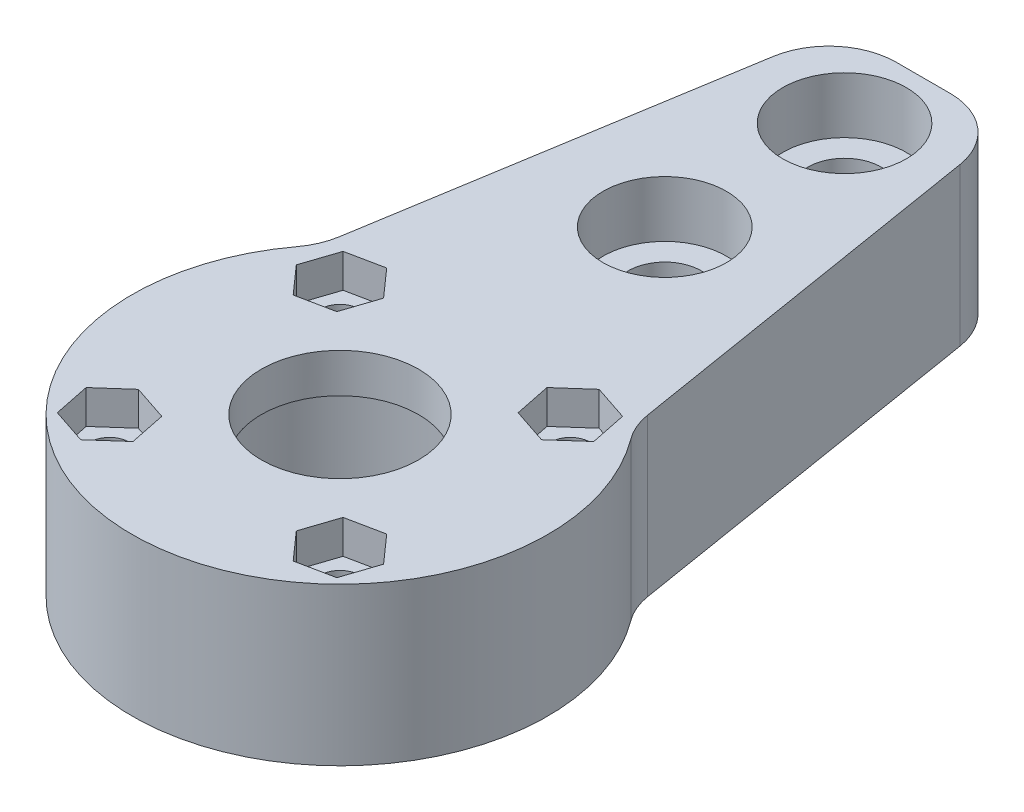
SolidWorks part; units mm, degrees
ref_plane "Front Plane" through (0, 0, 0) normal (0, 0, 1) x (1, 0, 0)
ref_plane "Top Plane" through (0, 0, 0) normal (0, 1, 0) x (1, 0, 0)
ref_plane "Right Plane" through (0, 0, 0) normal (1, 0, 0) x (0, 0, -1)
sketch "Sketch1" plane through (0, 0, 0) normal (0, 1, 0) x (1, 0, 0)
  line L0 (0, 0) -> (0, 16.3631) construction
  line L1 (-7.5, 16.9115) -> (7.5, 16.9115) construction
  line L2 (-7.5, 16.9115) -> (-7.5, 51.9115) construction
  line L3 (-7.5, 51.9115) -> (7.5, 51.9115)
  line L4 (7.5, 51.9115) -> (7.5, 16.9115) construction
  line L5 (12.7, 20) -> (-12.7, 20) construction
  line L6 (12.7721, 19.5576) -> (8.4504, 46.0788) construction
  line L7 (-12.7721, 19.5576) -> (-8.4504, 46.0788) construction
  line L8 (13.9857, 12.1099) -> (7.5, 51.9115)
  line L9 (-13.9857, 12.1099) -> (-7.5, 51.9115)
  circle A0 centre (0, 0) radius 7
  circle A1 centre (0, 0) radius 18.5 construction
  arc A2 (13.9857, 12.1099) -> (-13.9857, 12.1099) centre (0, 0) cw
  point P8 (0, 16.9115)
  point P15 (0, 20)
  dimension "D1" = 14
  dimension "D2" = 37
  dimension "D3" = 15
  dimension "D4" = 35
  dimension "D5" = 25.4
  dimension "D6" = 20
extrude "Boss-Extrude1" add sketch "Sketch1" along normal blind 14
sketch "Sketch2" plane through (0, 0, 0) normal (0, -1, 0) x (1, 0, 0)
  circle A0 centre (0, 0) radius 11.075
  dimension "D1" = 22.15
extrude "Cut-Extrude1" cut sketch "Sketch2" against normal blind 10.5
sketch "Sketch4" plane through (0, 0, 0) normal (0, -1, 0) x (1, 0, 0)
  line L0 (0, 0) -> (10.253, 10.253) construction
  line L1 (0, 0) -> (0, 5.0875) construction
  circle A1 centre (10.253, 10.253) radius 1.75
  circle A2 centre (10.253, -10.253) radius 1.75
  circle A3 centre (-10.253, -10.253) radius 1.75
  circle A4 centre (-10.253, 10.253) radius 1.75
  point P15 (0, 0)
  dimension "D1" = 45
  dimension "D2" = 3.5
  dimension "D3" = 14.5
  dimension "D4" = 4
extrude "Cut-Extrude4" cut sketch "Sketch4" against normal through all
sketch "Sketch5" plane through (0, 14, 0) normal (0, 1, 0) x (1, 0, 0)
  line L0 (13.3754, 9.2133) -> (12.7147, 12.4372)
  line L1 (-9.2133, 13.3754) -> (-12.4372, 12.7147)
  line L2 (-12.4372, 12.7147) -> (-13.4769, 9.5924)
  line L3 (-13.4769, 9.5924) -> (-11.2928, 7.1307)
  line L4 (-11.2928, 7.1307) -> (-8.0689, 7.7914)
  line L5 (-8.0689, 7.7914) -> (-7.0292, 10.9137)
  line L6 (-7.0292, 10.9137) -> (-9.2133, 13.3754)
  line L7 (12.7147, 12.4372) -> (9.5924, 13.4769)
  line L8 (9.5924, 13.4769) -> (7.1307, 11.2928)
  line L9 (7.1307, 11.2928) -> (7.7914, 8.0689)
  line L10 (7.7914, 8.0689) -> (10.9137, 7.0292)
  line L11 (10.9137, 7.0292) -> (13.3754, 9.2133)
  line L12 (9.2133, -13.3754) -> (12.4372, -12.7147)
  line L13 (12.4372, -12.7147) -> (13.4769, -9.5924)
  line L14 (13.4769, -9.5924) -> (11.2928, -7.1307)
  line L15 (11.2928, -7.1307) -> (8.0689, -7.7914)
  line L16 (8.0689, -7.7914) -> (7.0292, -10.9137)
  line L17 (7.0292, -10.9137) -> (9.2133, -13.3754)
  line L18 (-13.3754, -9.2133) -> (-12.7147, -12.4372)
  line L19 (-12.7147, -12.4372) -> (-9.5924, -13.4769)
  line L20 (-9.5924, -13.4769) -> (-7.1307, -11.2928)
  line L21 (-7.1307, -11.2928) -> (-7.7914, -8.0689)
  line L22 (-7.7914, -8.0689) -> (-10.9137, -7.0292)
  line L23 (-10.9137, -7.0292) -> (-13.3754, -9.2133)
  circle A0 centre (-10.253, 10.253) radius 3.25 construction
  circle A1 centre (10.253, 10.253) radius 3.25 construction
  circle A2 centre (10.253, -10.253) radius 3.25 construction
  circle A3 centre (-10.253, -10.253) radius 3.25 construction
  circle A4 centre (-10.253, 10.253) radius 2.85 construction
  circle A5 centre (10.253, 10.253) radius 3.25 construction
  circle A6 centre (10.253, 10.253) radius 2.85 construction
  circle A7 centre (10.253, -10.253) radius 3.25 construction
  circle A8 centre (10.253, -10.253) radius 2.85 construction
  circle A9 centre (-10.253, -10.253) radius 3.25 construction
  circle A10 centre (-10.253, -10.253) radius 2.85 construction
  point P12 (0, 0)
  point P47 (0, 0)
  dimension "D1" = 6.5
  dimension "D3" = 5.7
  dimension "D2" = 4
  dimension "D4" = 4
extrude "Cut-Extrude5" cut sketch "Sketch5" against normal blind 3
sketch "Sketch6" plane through (0, 14, 0) normal (0, 1, 0) x (1, 0, 0)
  line L0 (0, 51.9115) -> (0, 7) construction
  line L1 (7.5, 51.9115) -> (-7.5, 51.9115) construction
  circle A0 centre (0, 0) radius 7 construction
  circle A1 centre (0, 44.9115) radius 3.25
  circle A2 centre (0, 28.9115) radius 3.25
  dimension "D1" = 6.5
  dimension "D2" = 6.5
  dimension "D3" = 7
  dimension "D4" = 16
extrude "Cut-Extrude6" cut sketch "Sketch6" against normal through all
sketch "Sketch7" plane through (0, 14, 0) normal (0, 1, 0) x (1, 0, 0)
  circle A0 centre (0, 28.9115) radius 5.5
  circle A1 centre (0, 44.9115) radius 5.5
  dimension "D1" = 11
  dimension "D2" = 11
extrude "Cut-Extrude7" cut sketch "Sketch7" against normal blind 5
fillet "Fillet4" radius 6 4 edges at (13.9857, 7, -12.1099) (-13.9857, 7, -12.1099) (-7.5, 7, -51.9115) (7.5, 7, -51.9115)
